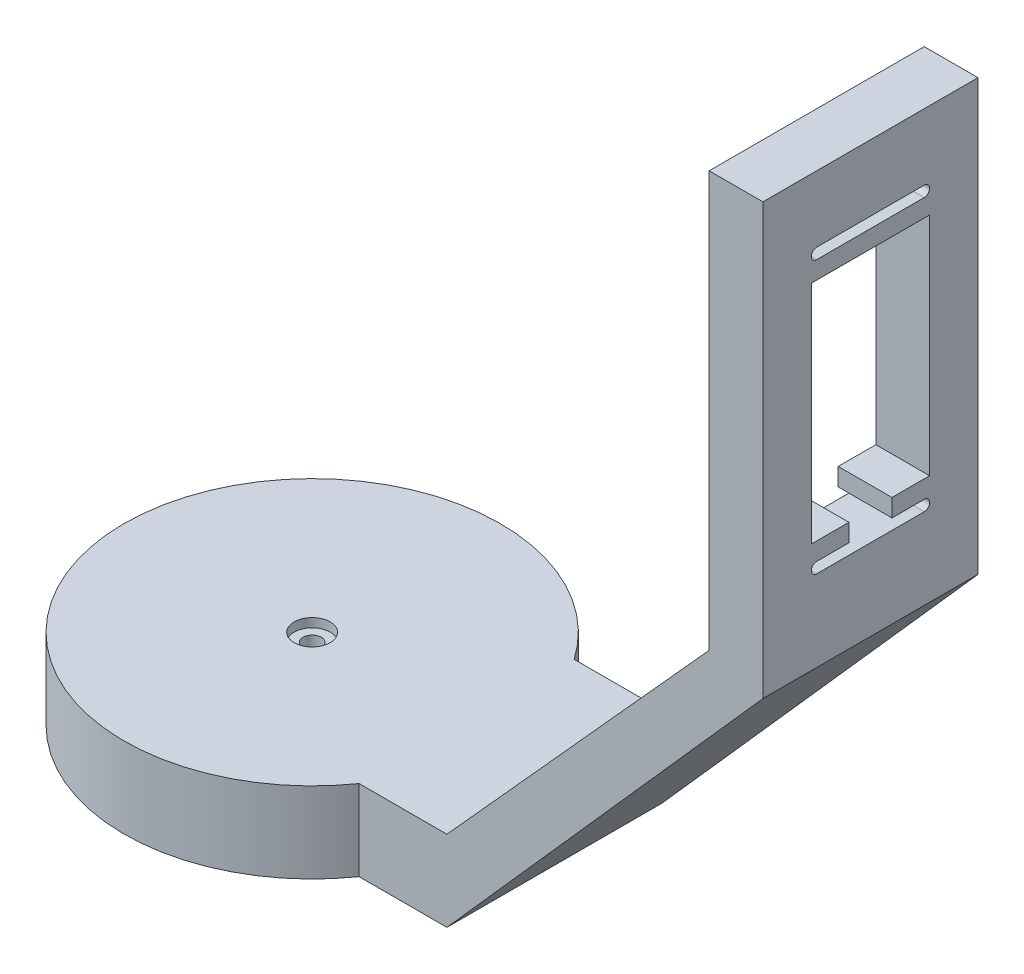
SolidWorks part; units mm, degrees
ref_plane "Front" through (0, 0, 0) normal (0, 0, 1) x (1, 0, 0)
ref_plane "Top" through (0, 0, 0) normal (0, 1, 0) x (1, 0, 0)
ref_plane "Right" through (0, 0, 0) normal (1, 0, 0) x (0, 0, -1)
sketch "草图1" plane through (0, 0, 0) normal (0, 1, 0) x (1, 0, 0)
  line L13 (0.0555, 20) -> (45.0555, 20)
  line L14 (0.0555, 20) -> (0.0555, -20)
  line L15 (0.0555, -20) -> (45.0555, -20)
  line L16 (45.0555, 20) -> (45.0555, -20)
  circle A1 centre (0, 0) radius 35
  dimension "D1" = 40
  dimension "D2" = 20
  dimension "D4" = 45
extrude "凸台-拉伸1" add sketch "草图1" along normal blind 15 contours A1 L15 L16 L13 | L15 A1 L13 L14 | L13 A1 L15 L14
sketch "草图2" plane through (0, 0, 20) normal (0, 0, 1) x (1, 0, 0)
  line L0 (45.0555, 0) -> (103.8194, 66.2288)
  line L1 (103.8194, 66.2288) -> (103.8194, 146.2288)
  line L2 (103.8194, 146.2288) -> (93.8194, 146.2288)
  line L3 (93.8194, 146.2288) -> (93.8194, 69.0094)
  line L5 (93.8194, 69.0094) -> (45.0555, 15)
  line L6 (45.0555, 15) -> (45.0555, 0)
  dimension "D1" = 10
  dimension "D2" = 80
extrude "凸台-拉伸2" add sketch "草图2" against normal blind 40 contours L2 L3 L5 L6 L0 L1
hole_wizard "1/4 六角头螺钉的柱形沉头孔base" positions "草图7" profile "草图8" counterbore size "M3" standard "ANSI Metric" end condition through all
sketch "草图7" plane through (0, 15, 0) normal (0, 1, 0) x (1, 0, 0)
  point P0 (0, 0)
sketch "草图8" plane through (0, 15, 0) normal (1, 0, 0) x (0, 0, 1)
  line L0 (0, 0) -> (0, 15)
  line L1 (0, 15) -> (1.7, 15)
  line L3 (1.7, 15) -> (1.7, 1.65)
  line L4 (1.7, 1.65) -> (3.35, 1.65)
  line L5 (3.35, 1.65) -> (3.35, 0)
  line L7 (3.35, 0) -> (0, 0)
  line L11 (0, -6.35) -> (0, 107.95) construction
  dimension "通孔孔直径" = 3.4
  dimension "通孔孔深度" = 15
  dimension "柱形沉头孔直径" = 6.7
  dimension "柱形沉头孔深度" = 1.65
sketch "草图10" plane through (0, 0, 20) normal (0, 0, 1) x (1, 0, 0)
sketch "草图11" plane through (103.8194, 0, 0) normal (1, 0, 0) x (0, 0, -1)
  line L1 (-11, 128.6188) -> (11, 128.6188)
  line L2 (-11, 128.6188) -> (-11, 86.6188)
  line L3 (-11, 86.6188) -> (11, 86.6188)
  line L4 (11, 128.6188) -> (11, 86.6188)
  line L5 (-20, 66.2288) -> (-20, 146.2288) construction
  line L7 (20, 146.2288) -> (-20, 146.2288) construction
  dimension "D1" = 22
  dimension "D2" = 42
  dimension "D3" = 9
  dimension "D4" = 17.61
extrude "切除-拉伸1" cut sketch "草图11" against normal blind 32
sketch "草图19" plane through (0, 0, 0) normal (0, -1, 0) x (1, 0, 0)
  line L0 (-29.939, 2.9835) -> (0, 6)
  line L1 (29.9255, 2.977) -> (0, 6)
  line L2 (29.8896, -3.02) -> (0, -6)
  line L3 (-30.0737, -4.2635) -> (0, -6)
  arc A2 (29.8896, -3.02) -> (29.9255, 2.977) centre (30, -0.022) ccw
  arc A3 (-30.0737, -4.2635) -> (-29.939, 2.9835) centre (-30, -0.6401) cw
  circle A4 centre (0, 0) radius 6
  dimension "D1" = 30
  dimension "D2" = 30
sketch "草图20" plane through (0, 0, 0) normal (0, -1, 0) x (1, 0, 0)
  line L0 (0, 6) -> (-10.4471, 4.9474)
  line L1 (-29.939, 2.9835) -> (0, 6) construction
  line L2 (-10.4471, 4.9474) -> (-10.4471, -5.3968)
  line L3 (-30.0737, -4.2635) -> (0, -6) construction
  line L4 (-10.4471, -5.3968) -> (0, -6)
  line L6 (0, -6) -> (10.4468, -4.9584)
  line L7 (29.8896, -3.02) -> (0, -6) construction
  line L8 (10.4468, -4.9584) -> (10.4468, 4.9447)
  line L9 (29.9255, 2.977) -> (0, 6) construction
  line L10 (10.4468, 4.9447) -> (0, 6)
  dimension "D1" = 10.5
  dimension "D2" = 10.5
extrude "切除-拉伸3" cut sketch "草图19" against normal blind 2 contours L1 L0 A3 L3 L2 A2
extrude "切除-拉伸4" cut sketch "草图20" against normal blind 3.5
sketch "草图21" plane through (103.8194, 0, 0) normal (1, 0, 0) x (0, 0, -1)
  line L0 (-10, 132.9188) -> (10, 132.9188) construction
  line L1 (-10, 133.9188) -> (10, 133.9188)
  line L2 (-10, 131.9188) -> (10, 131.9188)
  line L3 (11, 128.6188) -> (-11, 128.6188) construction
  line L4 (-20, 66.2288) -> (-20, 146.2288) construction
  line L5 (20, 66.2288) -> (20, 146.2288) construction
  line L6 (-10, 82.3188) -> (10, 82.3188) construction
  line L7 (-10, 83.3188) -> (10, 83.3188)
  line L8 (-10, 81.3188) -> (10, 81.3188)
  line L9 (-11, 86.6188) -> (11, 86.6188) construction
  arc A0 (-10, 133.9188) -> (-10, 131.9188) centre (-10, 132.9188) ccw
  arc A1 (10, 131.9188) -> (10, 133.9188) centre (10, 132.9188) ccw
  arc A2 (-10, 83.3188) -> (-10, 81.3188) centre (-10, 82.3188) ccw
  arc A3 (10, 81.3188) -> (10, 83.3188) centre (10, 82.3188) ccw
  point P2 (0, 132.9188)
  point P15 (0, 82.3188)
  dimension "D1" = 3.3
  dimension "D2" = 2
  dimension "D3" = 10
  dimension "D4" = 10
  dimension "D5" = 2
  dimension "D6" = 3.3
extrude "切除-拉伸5" cut sketch "草图21" against normal blind 20
sketch "草图22" plane through (103.8194, 0, 0) normal (1, 0, 0) x (0, 0, -1)
  line L0 (-11, 86.6188) -> (11, 86.6188) construction
  line L1 (-4, 86.6188) -> (4, 86.6188)
  line L2 (-4, 86.6188) -> (-4, 83.3188)
  line L3 (-4, 83.3188) -> (4, 83.3188)
  line L4 (4, 86.6188) -> (4, 83.3188)
  line L5 (10, 83.3188) -> (-10, 83.3188) construction
  line L6 (-11, 128.6188) -> (-11, 86.6188) construction
  line L7 (11, 86.6188) -> (11, 128.6188) construction
  dimension "D1" = 7
  dimension "D2" = 7
extrude "切除-拉伸6" cut sketch "草图22" against normal blind 20
